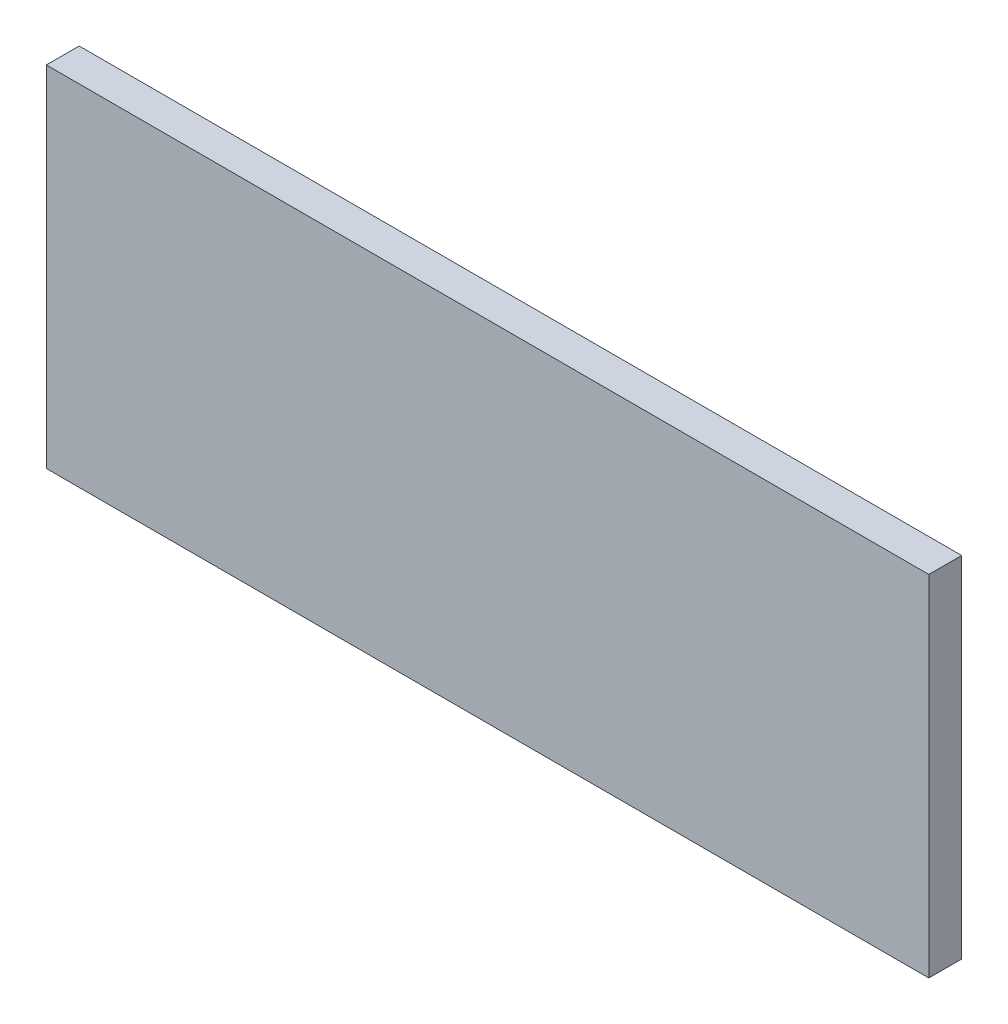
SolidWorks part; units mm, degrees
ref_plane "Front Plane" through (0, 0, 0) normal (0, 0, 1) x (1, 0, 0)
ref_plane "Top Plane" through (0, 0, 0) normal (0, 1, 0) x (1, 0, 0)
ref_plane "Right Plane" through (0, 0, 0) normal (1, 0, 0) x (0, 0, -1)
sketch "Sketch1" plane through (0, 0, 14.9278) normal (0, 0, 1) x (1, 0, 0)
  line L1 (12.0488, 48.3973) -> (38.9193, 48.3973)
  line L2 (12.0488, 48.3973) -> (12.0488, 59.0393)
  line L3 (12.0488, 59.0393) -> (38.9193, 59.0393)
  line L4 (38.9193, 48.3973) -> (38.9193, 59.0393)
  line L5 (12.0488, 48.3973) -> (38.9193, 59.0393) construction
  line L6 (12.0488, 59.0393) -> (38.9193, 48.3973) construction
  point P0 (25.484, 53.7183)
extrude "Boss-Extrude1" add sketch "Sketch1" along normal blind 1
ref_point "ScreenCenter"
